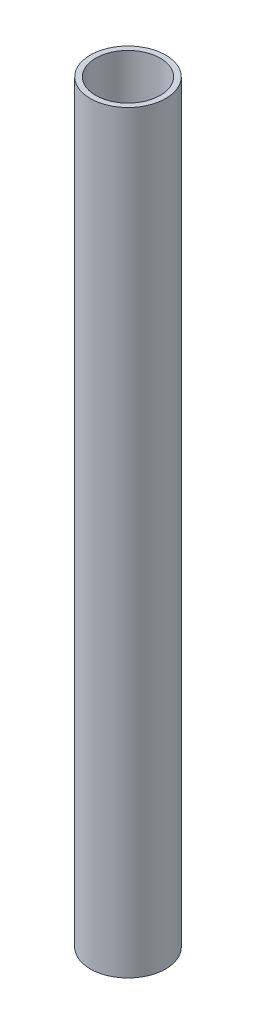
SolidWorks part; units mm, degrees
material "Сплав 2024"
ref_plane "Front" through (0, 0, 0) normal (0, 0, 1) x (1, 0, 0)
ref_plane "Top" through (0, 0, 0) normal (0, 1, 0) x (1, 0, 0)
ref_plane "Right" through (0, 0, 0) normal (1, 0, 0) x (0, 0, -1)
sketch "Эскиз1" plane through (0, 0, 0) normal (0, 1, 0) x (1, 0, 0)
  circle A0 centre (0, 0) radius 7
  circle A1 centre (0, 0) radius 6
  dimension "D1" = 14
  dimension "D2" = 12
extrude "Бобышка-Вытянуть1" add sketch "Эскиз1" along normal blind 140
